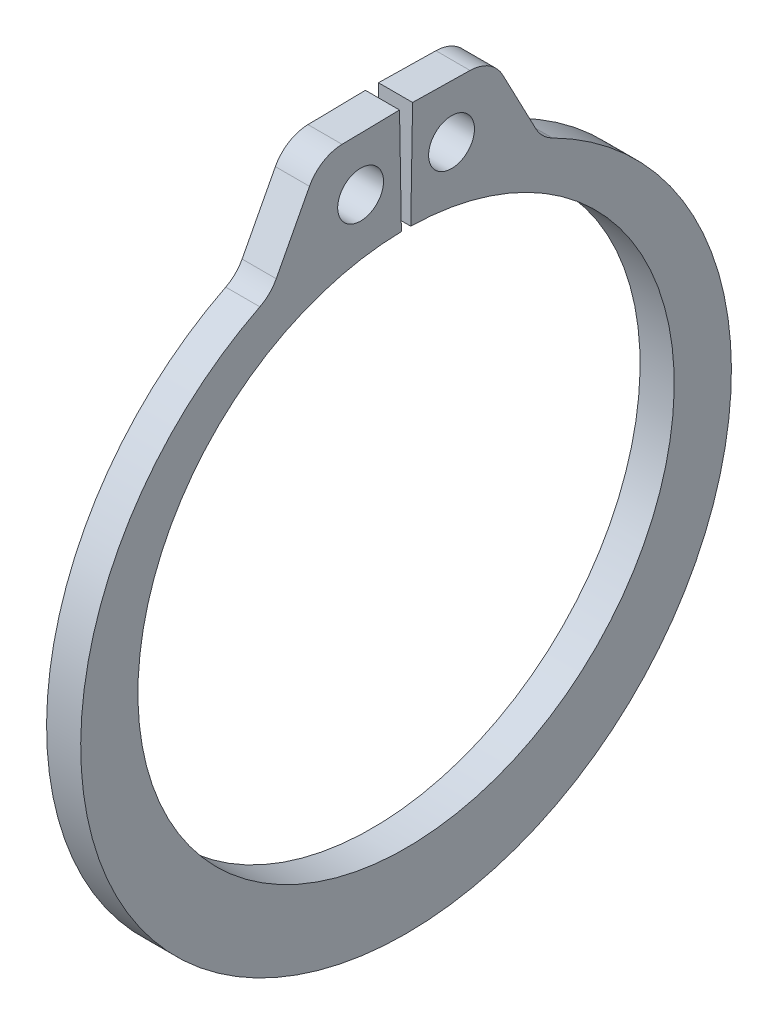
SolidWorks part; units mm, degrees
material "Cast Carbon Steel"
ref_plane "Front" through (0, 0, 0) normal (0, 0, 1) x (1, 0, 0)
ref_plane "Top" through (0, 0, 0) normal (0, 1, 0) x (1, 0, 0)
ref_plane "Right" through (0, 0, 0) normal (1, 0, 0) x (0, 0, -1)
sketch "Sketch1" plane through (0, 0, 0) normal (1, 0, 0) x (0, 0, -1)
  line L0 (0, 0) -> (0, 6.985) construction
  line L1 (-0.1219, 6.9839) -> (-0.1702, 9.7521)
  line L2 (0.1702, 9.7521) -> (2.2464, 9.7159)
  line L3 (2.2464, 9.7159) -> (3.5321, 7.264)
  line L4 (0.1219, 6.9839) -> (0.1702, 9.7521)
  line L5 (-0.1702, 9.7521) -> (-2.2464, 9.7159)
  line L6 (-2.2464, 9.7159) -> (-3.5321, 7.264)
  line L7 (-3.5321, 7.264) -> (-3.0545, 6.2817) construction
  line L8 (3.5321, 7.264) -> (3.0545, 6.2817) construction
  line L9 (0, -6.985) -> (0, -8.9154) construction
  line L10 (-2.2464, 9.7159) -> (-0.1219, 6.9839) construction
  line L11 (0, 6.985) -> (0, 9.7536) construction
  line L12 (-6.985, 0) -> (6.985, 0) construction
  circle A0 centre (0, 0) radius 6.985 construction
  arc A1 (-0.1219, 6.9839) -> (0.1219, 6.9839) centre (0, 0) ccw
  circle A3 centre (0, 0) radius 10.7315 construction
  circle A4 centre (-1.1841, 8.3499) radius 0.5969
  circle A5 centre (1.1841, 8.3499) radius 0.5969
  arc A6 (-3.5321, 7.264) -> (3.5321, 7.264) centre (0, -0.4402) ccw
  point P0 (0, -8.9154)
  dimension "A" = 13.97
  dimension "D2" = 2.0764
  dimension "L" = 21.463
  dimension "Hole" = 1.1938
  dimension "Smin" = 1.0922
  dimension "Smax" = 1.9304
  dimension "H" = 2.7686
  dimension "Angle" = 1
extrude "Extrude1" add sketch "Sketch1" along normal mid plane 0.889
fillet "Fillet1" radius 0.9779 4 edges at (0, 7.264, 3.5321) (0, 7.264, -3.5321) (0, 9.7159, 2.2464) (0, 9.7159, -2.2464)
sketch "Sketch2" plane through (0, 0, 0) normal (0, 0, 1) x (1, 0, 0)
  line L0 (-4.9403, 0) -> (12.8397, 0)
  line L1 (12.8397, 0) -> (12.8397, -7.5438)
  line L2 (-0.4953, -7.5438) -> (-4.4958, -7.5438)
  line L3 (12.8397, -7.5438) -> (0.4953, -7.5438)
  line L4 (0.4953, -7.5438) -> (0.4953, -7.0993)
  line L5 (0.4953, -7.0993) -> (-0.4953, -7.0993)
  line L6 (-0.4953, -7.0993) -> (-0.4953, -7.5438)
  line L7 (-0.4953, -7.5438) -> (-4.9403, -7.5438) construction
  line L8 (-4.9403, -7.5438) -> (-4.9403, 0) construction
  line L9 (12.8397, 0) -> (76.391, 0) construction
  line L10 (-4.4958, -7.5438) -> (-4.9403, -7.0993)
  line L11 (-4.9403, -7.0993) -> (-4.9403, 0)
  point P10 (0, -7.0993)
  dimension "D1" = 45
  dimension "Dg" = 14.1986
  dimension "Ds" = 15.0876
  dimension "W" = 0.9906
  dimension "D2" = 17.78
  dimension "D3" = 4.445
revolve "Revolve1" [suppressed] add sketch "Sketch2" angle 360 about L9
delete or keep bodies "Body-Delete1" [suppressed] type delete bodies bodies 122
equation "\"D2@Sketch2\" = \"D1@Extrude1\"*20"
equation "\"D3@Sketch2\" = \"D2@Sketch2\"/4"
equation "\"D2@Sketch1\" = \"H@Sketch1\"*.75"
